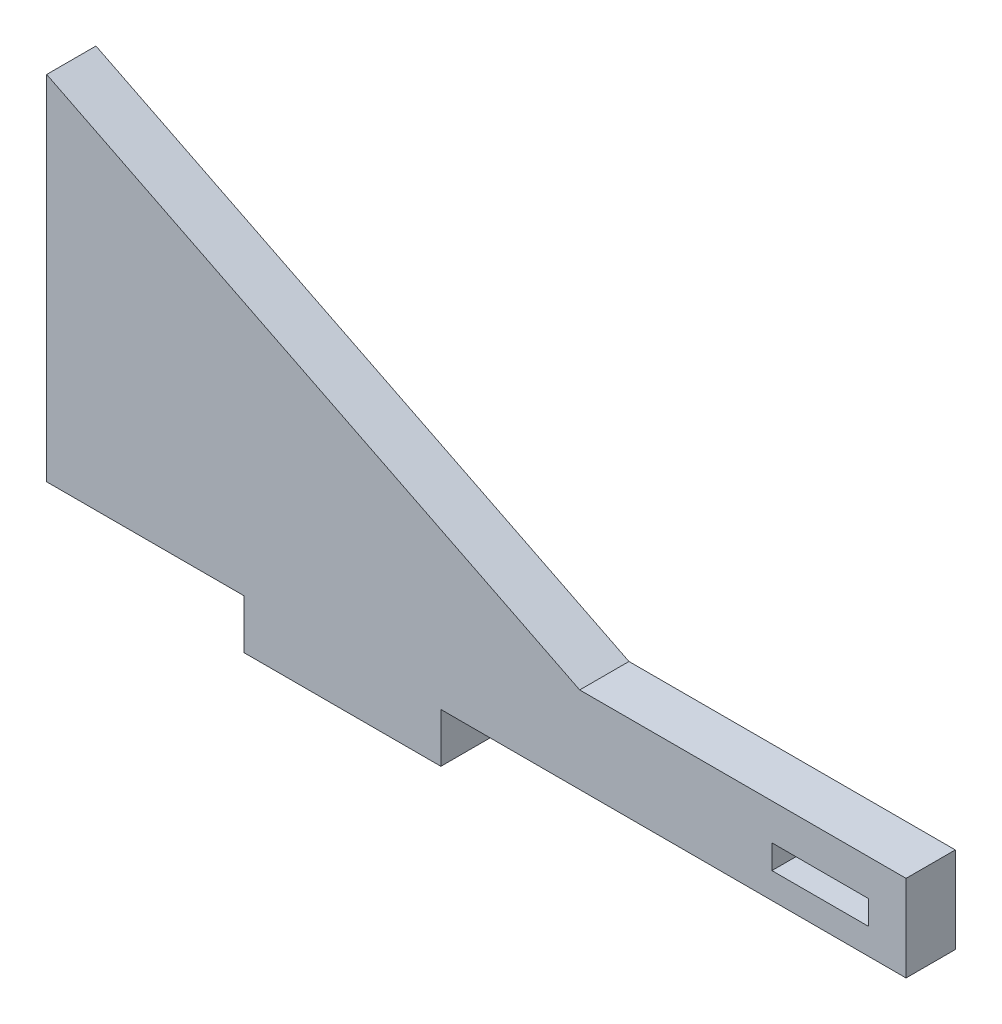
SolidWorks part; units mm, degrees
ref_plane "Front Plane" through (0, 0, 0) normal (0, 0, 1) x (1, 0, 0)
ref_plane "Top Plane" through (0, 0, 0) normal (0, 1, 0) x (1, 0, 0)
ref_plane "Right Plane" through (0, 0, 0) normal (1, 0, 0) x (0, 0, -1)
sketch "Sketch1" plane through (0, 0, 0) normal (0, 0, 1) x (1, 0, 0)
  line L0 (38.1, -20.066) -> (38.1, -12.7) construction
  line L1 (-38.1, -20.066) -> (-12.7, -20.066)
  line L2 (38.1, -12.7) -> (38.1, -20.066)
  line L3 (12.7, -26.416) -> (-12.7, -26.416)
  line L4 (-38.1, 25.4) -> (-38.1, -20.066)
  line L5 (5.4429, 3.6286) -> (-30.099, -20.066) construction
  line L6 (30.099, -20.066) -> (-38.1, 25.4) construction
  line L7 (-38.1, 25.4) -> (38.1, -12.7)
  line L9 (12.7, -20.066) -> (38.1, -20.066)
  line L10 (-12.7, -20.066) -> (-12.7, -26.416)
  line L11 (12.7, -20.066) -> (12.7, -26.416)
  point P0 (0, 0)
  dimension "D1" = 6.35
extrude "Boss-Extrude1" add sketch "Sketch1" along normal blind 6.35
sketch "Sketch2" plane through (0, 0, 6.35) normal (0, 0, 1) x (1, 0, 0)
  line L0 (38.1, -20.066) -> (72.644, -20.066)
  line L1 (72.644, -12.7) -> (72.644, -8.9443) construction
  line L2 (72.644, -20.066) -> (72.644, -12.7)
  line L3 (-38.1, -20.066) -> (72.644, -20.066) construction
  line L4 (72.644, -8.9443) -> (30.5885, -8.9443) construction
  line L5 (38.1, -12.7) -> (-38.1, 25.4) construction
  line L6 (30.5885, -8.9443) -> (72.644, -8.9443)
  line L7 (30.5885, -8.9443) -> (38.1, -12.7)
  line L8 (72.644, -12.7) -> (72.644, -8.9443)
  line L12 (-38.1, 25.4) -> (-38.1, -20.066)
  line L13 (-38.1, -20.066) -> (-12.7, -20.066)
  line L14 (-12.7, -20.066) -> (-12.7, -26.416)
  line L15 (-12.7, -26.416) -> (12.7, -26.416)
  line L16 (12.7, -26.416) -> (12.7, -20.066)
  line L17 (12.7, -20.066) -> (38.1, -20.066)
  line L18 (38.1, -20.066) -> (38.1, -12.7)
  line L19 (38.1, -12.7) -> (-38.1, 25.4)
  line L26 (38.1, -20.066) -> (38.1, -12.7)
  dimension "D1" = 110.744
  dimension "D2" = 0
extrude "Boss-Extrude2" add sketch "Sketch2" against normal through all
sketch "Sketch4" plane through (0, 0, 0) normal (0, 0, -1) x (-1, 0, 0)
  line L1 (-67.7758, -16.7235) -> (-55.3561, -16.7235)
  line L2 (-67.7758, -16.7235) -> (-67.7758, -13.6212)
  line L3 (-67.7758, -13.6212) -> (-55.3561, -13.6212)
  line L4 (-55.3561, -16.7235) -> (-55.3561, -13.6212)
  line L5 (-55.3561, -15.1724) -> (-72.644, -15.1724) construction
  line L6 (-72.644, -20.066) -> (-72.644, -8.9443) construction
extrude "Cut-Extrude1" cut sketch "Sketch4" against normal through all
equation "\"D1@Sketch1\" = \"Material\""
equation "\"Material\"= \"GMaterial@Platform.assembly\""
equation "\"D1@Boss-Extrude1\" = \"Material\""
